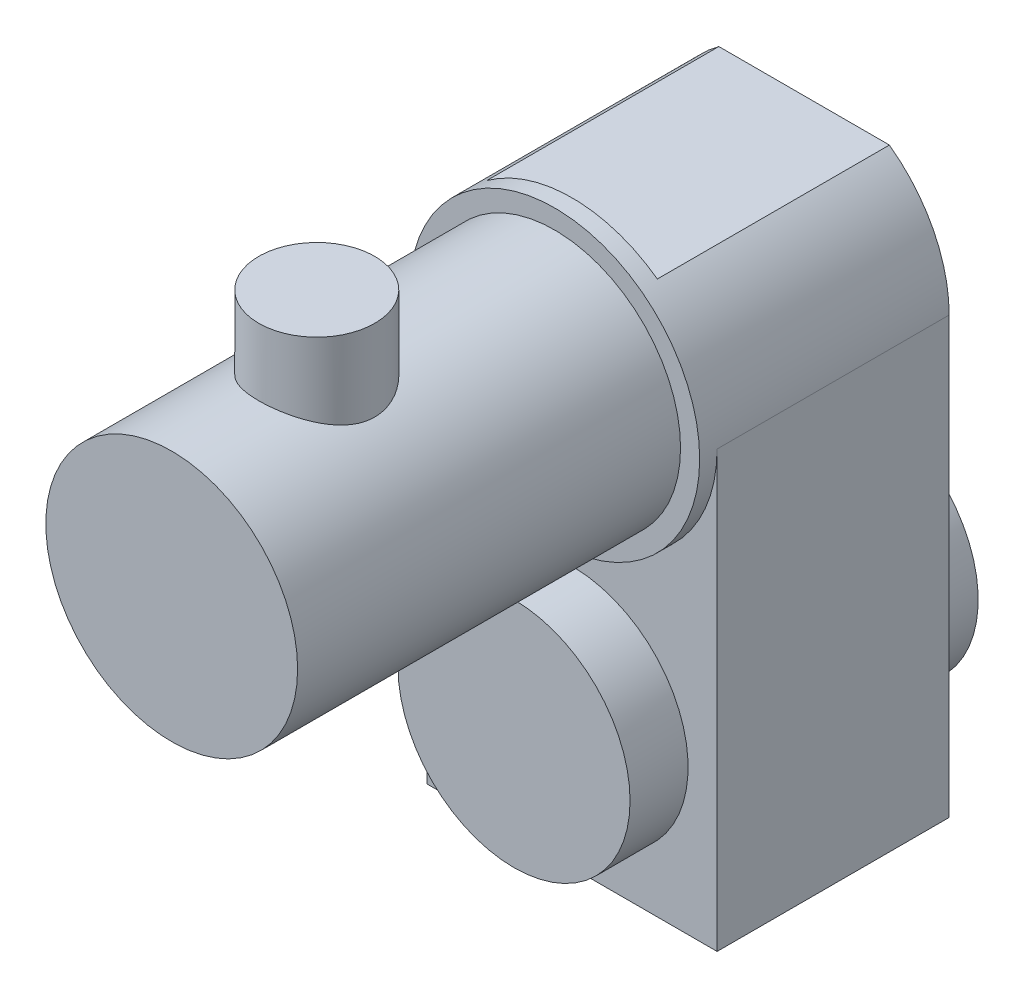
SolidWorks part; units mm, degrees
ref_plane "前视基准面" through (0, 0, 0) normal (0, 0, 1) x (1, 0, 0)
ref_plane "上视基准面" through (0, 0, 0) normal (0, 1, 0) x (1, 0, 0)
ref_plane "右视基准面" through (0, 0, 0) normal (1, 0, 0) x (0, 0, -1)
sketch "草图1" plane through (0, 0, 0) normal (0, 0, 1) x (1, 0, 0)
  circle A0 centre (0, 0) radius 125
  dimension "D1" = 250
extrude "凸台-拉伸1" add sketch "草图1" along normal blind 15
sketch "草图2" plane through (0, 0, 15) normal (0, 0, 1) x (1, 0, 0)
  circle A0 centre (0, 0) radius 108.5
  dimension "D1" = 217
extrude "凸台-拉伸2" add sketch "草图2" along normal blind 330
ref_plane "基准面1" through (0, 0, 220) normal (0, 0, 1) x (1, 0, 0)
sketch "草图4" plane through (0, 0, 220) normal (0, 0, 1) x (1, 0, 0)
  line L0 (0, 165.767) -> (0, 0) construction
  line L1 (-50, 96.2925) -> (-50, 166.2925)
  line L2 (-50, 166.2925) -> (0, 166.2925)
  line L3 (0, 166.2925) -> (0, 96.2925)
  line L4 (0, 96.2925) -> (-50, 96.2925)
  circle A0 centre (0, 0) radius 108.5 construction
  dimension "D1" = 50
  dimension "D2" = 70
revolve "旋转1" add sketch "草图4" angle 360 about L0
sketch "草图5" plane through (0, 0, 0) normal (0, 0, -1) x (-1, 0, 0)
  line L0 (-179.1522, 0) -> (203.7346, 0) construction
  line L1 (0, 178.0784) -> (0, -214.651) construction
  line L2 (-73.4964, 101.1102) -> (73.4964, 101.1102)
  line L3 (-125, 0) -> (-125, -375)
  line L4 (-125, -375) -> (125, -375)
  line L5 (125, -375) -> (125, 0)
  circle A0 centre (0, 0) radius 125 construction
  arc A1 (-73.4964, 101.1102) -> (-125, 0) centre (0, 0) ccw
  arc A2 (125, 0) -> (73.4964, 101.1102) centre (0, 0) ccw
  dimension "D1" = 375
extrude "凸台-拉伸4" add sketch "草图5" along normal blind 200
sketch "草图6" plane through (0, 0, -200) normal (0, 0, -1) x (-1, 0, 0)
  circle A0 centre (0, -250) radius 100
  dimension "D2" = 200
  dimension "D1" = 250
extrude "凸台-拉伸5" add sketch "草图6" along normal blind 50
sketch "草图7" plane through (0, 0, 0) normal (0, 0, 1) x (1, 0, 0)
  circle A0 centre (0, -250) radius 100
  dimension "D2" = 200
  dimension "D1" = 250
extrude "凸台-拉伸6" add sketch "草图7" along normal blind 50
